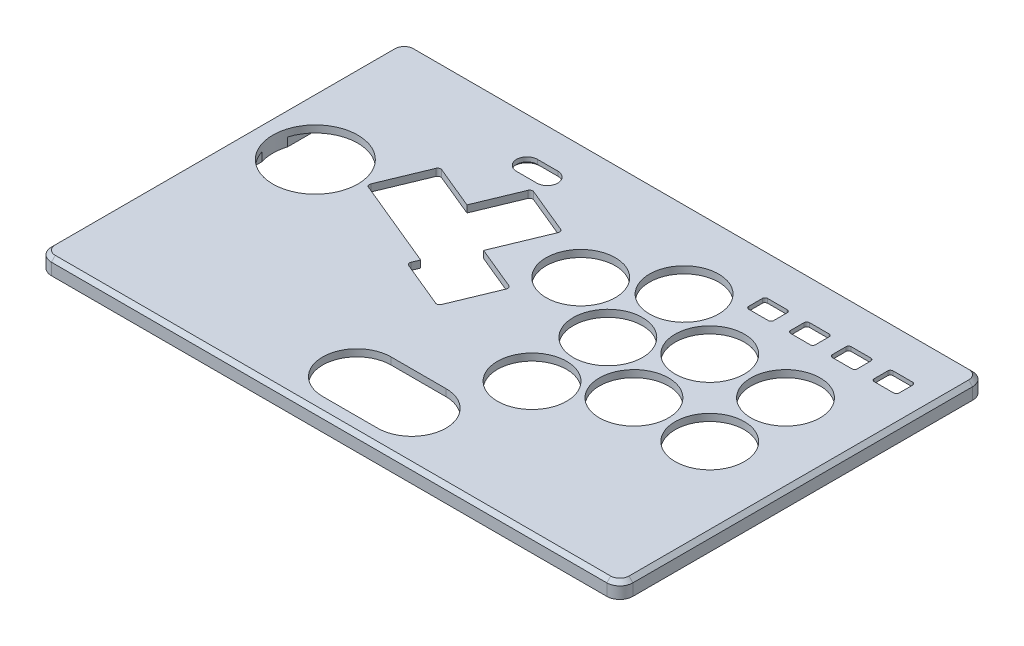
SolidWorks part; units mm, degrees
ref_plane "Front Plane" through (0, 0, 0) normal (0, 0, 1) x (1, 0, 0)
ref_plane "Top Plane" through (0, 0, 0) normal (0, 1, 0) x (1, 0, 0)
ref_plane "Right Plane" through (0, 0, 0) normal (1, 0, 0) x (0, 0, -1)
sketch "Sketch1" plane through (0, 0, 0) normal (0, 1, 0) x (1, 0, 0)
  line L1 (0, 0) -> (222.53, 0)
  line L2 (0, 0) -> (0, 140)
  line L3 (0, 140) -> (222.53, 140)
  line L4 (222.53, 0) -> (222.53, 140)
  line L5 (217.53, 140) -> (50.88, 140) construction
  line L6 (222.53, 5) -> (222.53, 135) construction
extrude "Top Plate" add sketch "Sketch1" along normal blind 6
fillet "Corner Fillet" radius 5 4 edges at (0, 3, -140) (0, 3, 0) (222.53, 3, -140) (222.53, 3, 0)
hole_wizard "M3 Clearance Hole1" positions "3DSketch1" profile "Sketch3" hole size "M3" standard "ANSI Metric"
sketch3d "3DSketch1"
  line L0 (5, 0, 0) -> (217.53, 0, 0) construction
  line L1 (222.53, 0, -5) -> (222.53, 0, -135) construction
  line L2 (217.53, 0, -140) -> (5, 0, -140) construction
  line L3 (0, 0, -135) -> (0, 0, -5) construction
  point P0 (217.03, 0, -5.5)
  point P2 (217.03, 0, -134.5)
  point P4 (5.5, 0, -134.5)
  point P6 (5.5, 0, -5.5)
  dimension "D1" = 5.5
  dimension "D2" = 5.5
  dimension "D3" = 5.5
  dimension "D4" = 5.5
  dimension "D5" = 5.5
  dimension "D6" = 5.5
  dimension "D7" = 5.5
  dimension "D8" = 5.5
sketch "Sketch3" plane through (217.03, 0, -5.5) normal (1, 0, 0) x (0, 0, -1)
  line L0 (0, 0) -> (0, 5.25)
  line L1 (0, 5.25) -> (1.7, 4.2285)
  line L2 (1.7, 4.2285) -> (1.7, 0)
  line L5 (1.7, 0) -> (0, 0)
  line L10 (0, 5.25) -> (-1.7, 4.2285) construction
  line L11 (0, -6.35) -> (0, 107.95) construction
  dimension "Hole Dia." = 3.4
  dimension "Hole Depth" = 5.25
  dimension "Drill Angle" = 118
sketch "Sketch4" plane through (0, 6, 0) normal (0, -1, 0) x (-1, 0, 0)
  line L0 (-94.0588, 59.555) -> (-76.4589, 66.8451) construction
  line L1 (-94.0588, 59.555) -> (-101.349, 77.1549) construction
  line L2 (-76.4589, 66.8451) -> (-77.9897, 70.5406) construction
  line L3 (-101.349, 77.1549) -> (-83.7491, 84.445) construction
  line L4 (-94.0588, 59.555) -> (-83.7491, 84.445) construction
  line L5 (-76.4589, 66.8451) -> (-101.349, 77.1549) construction
  line L6 (-77.9897, 70.5406) -> (-60.3898, 77.8307) construction
  line L7 (-83.7491, 84.445) -> (-85.2798, 88.1405) construction
  line L8 (-60.3898, 77.8307) -> (-67.6799, 95.4306) construction
  line L9 (-85.2798, 88.1405) -> (-67.6799, 95.4306) construction
  line L10 (-77.9897, 70.5406) -> (-67.6799, 95.4306) construction
  line L11 (-60.3898, 77.8307) -> (-85.2798, 88.1405) construction
  line L12 (-60.3898, 77.8307) -> (-42.7899, 85.1209) construction
  line L14 (-42.7899, 85.1209) -> (-50.08, 102.7208) construction
  line L15 (-67.6799, 95.4306) -> (-50.08, 102.7208) construction
  line L16 (-60.3898, 77.8307) -> (-50.08, 102.7208) construction
  line L17 (-42.7899, 85.1209) -> (-67.6799, 95.4306) construction
  line L19 (-67.6799, 95.4306) -> (-74.97, 113.0306) construction
  line L20 (-85.2798, 88.1405) -> (-92.5699, 105.7404) construction
  line L21 (-74.97, 113.0306) -> (-92.5699, 105.7404) construction
  line L22 (-67.6799, 95.4306) -> (-92.5699, 105.7404) construction
  line L23 (-85.2798, 88.1405) -> (-74.97, 113.0306) construction
  line L24 (-5, 0) -> (-217.53, 0) construction
  line L25 (-59.9305, 76.7221) -> (-42.3306, 84.0122)
  line L26 (-41.6812, 85.5801) -> (-48.9713, 103.18)
  line L27 (-67.0304, 96.9985) -> (-50.5392, 103.8294)
  line L28 (-67.0304, 96.9985) -> (-73.8613, 113.4898)
  line L29 (-75.4292, 114.1392) -> (-93.0291, 106.8491)
  line L30 (-86.3884, 87.6813) -> (-93.6786, 105.2812)
  line L31 (-85.3169, 85.0944) -> (-86.3884, 87.6813)
  line L32 (-101.8082, 78.2635) -> (-85.3169, 85.0944)
  line L33 (-95.1675, 59.0958) -> (-102.4576, 76.6957)
  line L34 (-93.5996, 58.4463) -> (-75.9997, 65.7365)
  line L35 (-75.3503, 67.3043) -> (-76.4218, 69.8912)
  line L36 (-76.4218, 69.8912) -> (-59.9305, 76.7221)
  line L37 (-66.5712, 95.8899) -> (-74.3206, 114.5984) construction
  line L38 (-68.1391, 96.5393) -> (-49.4305, 104.2886) construction
  line L39 (-74.3206, 114.5984) -> (-94.1378, 106.3899) construction
  line L40 (-86.3884, 87.6813) -> (-94.1378, 106.3899) construction
  line L41 (-102.9168, 77.8043) -> (-85.3169, 85.0944) construction
  line L42 (-94.7083, 57.9871) -> (-102.9168, 77.8043) construction
  line L43 (-94.7083, 57.9871) -> (-74.8911, 66.1957) construction
  line L44 (-74.8911, 66.1957) -> (-76.4218, 69.8912) construction
  line L45 (-59.9305, 76.7221) -> (-41.222, 84.4714) construction
  line L46 (-41.222, 84.4714) -> (-49.4305, 104.2886) construction
  line L47 (-123.9039, 19) -> (-102.9039, 19) construction
  line L48 (-123.9039, 32.1) -> (-102.9039, 32.1)
  line L49 (-123.9039, 5.9) -> (-102.9039, 5.9)
  circle A0 centre (-23, 83.0083) radius 16.25
  circle A1 centre (-137.9339, 51) radius 13.25
  circle A2 centre (-162.9339, 65) radius 13.25
  circle A3 centre (-191.9339, 65) radius 13.25
  circle A4 centre (-191.9339, 94) radius 13.25
  circle A5 centre (-162.9339, 94) radius 13.25
  circle A6 centre (-137.9339, 80) radius 13.25
  circle A7 centre (-138.1143, 108.9994) radius 13.25
  circle A8 centre (-112.9159, 94.6459) radius 13.25
  arc A9 (-93.0291, 106.8491) -> (-93.6786, 105.2812) centre (-92.5699, 105.7404) ccw
  arc A10 (-101.8082, 78.2635) -> (-102.4576, 76.6957) centre (-101.349, 77.1549) ccw
  arc A11 (-95.1675, 59.0958) -> (-93.5996, 58.4463) centre (-94.0588, 59.555) ccw
  arc A12 (-75.9997, 65.7365) -> (-75.3503, 67.3043) centre (-76.4589, 66.8451) ccw
  arc A13 (-42.3306, 84.0122) -> (-41.6812, 85.5801) centre (-42.7899, 85.1209) ccw
  arc A14 (-73.8613, 113.4898) -> (-75.4292, 114.1392) centre (-74.97, 113.0306) ccw
  arc A15 (-48.9713, 103.18) -> (-50.5392, 103.8294) centre (-50.08, 102.7208) ccw
  arc A16 (-123.9039, 32.1) -> (-123.9039, 5.9) centre (-123.9039, 19) ccw
  arc A17 (-102.9039, 5.9) -> (-102.9039, 32.1) centre (-102.9039, 19) ccw
  point P28 (-88.9039, 72)
  point P29 (-72.8348, 82.9856)
  point P30 (-55.2349, 90.2758)
  point P35 (-80.1249, 100.5855)
  point P90 (-113.4039, 19)
  point P96 (-89.8039, 19)
  point P97 (-137.0039, 19)
  dimension "D1" = 32.5
  dimension "D2" = 26.5
  dimension "D6" = 1.2
  dimension "D8" = 13.1
  dimension "D3" = 22.5
  dimension "D4" = 19.05
  dimension "D5" = 1.2
  dimension "D7" = 47.2
extrude "Primary Buttons" cut sketch "Sketch4" along normal blind 10 contours A15 L26 A13 L25 L36 L35 A12 L34 A11 L33 A10 L32 L31 L30 A9 L29 A14 L28 L27 | A0 | A8 | A7 | A5 | A4 | A6 | A1 | A2 | A3 | A17 L49 A16 L48
sketch "Sketch5" plane through (0, 0, 0) normal (0, -1, 0) x (1, 0, 0)
  line L2 (154.55, -122.52) -> (154.55, -117.32)
  line L3 (155.55, -116.32) -> (163.05, -116.32)
  line L4 (164.05, -122.52) -> (164.05, -117.32)
  line L5 (154.55, -123.52) -> (164.05, -116.32) construction
  line L6 (154.55, -116.32) -> (164.05, -123.52) construction
  line L7 (155.55, -123.52) -> (163.05, -123.52)
  line L8 (170.55, -122.52) -> (170.55, -117.32)
  line L9 (171.55, -116.32) -> (179.05, -116.32)
  line L10 (180.05, -122.52) -> (180.05, -117.32)
  line L11 (171.55, -123.52) -> (179.05, -123.52)
  line L12 (170.55, -123.52) -> (180.05, -116.32) construction
  line L13 (170.55, -116.32) -> (180.05, -123.52) construction
  line L14 (186.55, -122.52) -> (186.55, -117.32)
  line L15 (187.55, -116.32) -> (195.05, -116.32)
  line L16 (196.05, -122.52) -> (196.05, -117.32)
  line L17 (187.55, -123.52) -> (195.05, -123.52)
  line L18 (186.55, -123.52) -> (196.05, -116.32) construction
  line L19 (186.55, -116.32) -> (196.05, -123.52) construction
  line L20 (202.55, -122.52) -> (202.55, -117.32)
  line L21 (203.55, -116.32) -> (211.05, -116.32)
  line L22 (212.05, -122.52) -> (212.05, -117.32)
  line L23 (203.55, -123.52) -> (211.05, -123.52)
  line L24 (202.55, -123.52) -> (212.05, -116.32) construction
  line L25 (202.55, -116.32) -> (212.05, -123.52) construction
  line L26 (159.3, -119.92) -> (160, -119.92) construction
  arc A0 (163.05, -123.52) -> (164.05, -122.52) centre (163.05, -122.52) ccw
  arc A1 (155.55, -123.52) -> (154.55, -122.52) centre (155.55, -122.52) cw
  arc A2 (154.55, -117.32) -> (155.55, -116.32) centre (155.55, -117.32) cw
  arc A3 (163.05, -116.32) -> (164.05, -117.32) centre (163.05, -117.32) cw
  arc A4 (179.05, -123.52) -> (180.05, -122.52) centre (179.05, -122.52) ccw
  arc A5 (171.55, -123.52) -> (170.55, -122.52) centre (171.55, -122.52) cw
  arc A6 (170.55, -117.32) -> (171.55, -116.32) centre (171.55, -117.32) cw
  arc A7 (179.05, -116.32) -> (180.05, -117.32) centre (179.05, -117.32) cw
  arc A8 (195.05, -123.52) -> (196.05, -122.52) centre (195.05, -122.52) ccw
  arc A9 (187.55, -123.52) -> (186.55, -122.52) centre (187.55, -122.52) cw
  arc A10 (186.55, -117.32) -> (187.55, -116.32) centre (187.55, -117.32) cw
  arc A11 (195.05, -116.32) -> (196.05, -117.32) centre (195.05, -117.32) cw
  arc A12 (211.05, -123.52) -> (212.05, -122.52) centre (211.05, -122.52) ccw
  arc A13 (203.55, -123.52) -> (202.55, -122.52) centre (203.55, -122.52) cw
  arc A14 (202.55, -117.32) -> (203.55, -116.32) centre (203.55, -117.32) cw
  arc A15 (211.05, -116.32) -> (212.05, -117.32) centre (211.05, -117.32) cw
  point P0 (159.3, -119.92)
  point P7 (175.3, -119.92)
  point P39 (191.3, -119.92)
  point P56 (207.3, -119.92)
  dimension "D1" = 7.2
  dimension "D3" = 1
  dimension "D2" = 9.5
  dimension "D5" = 16
  dimension "D6" = 0.7
  dimension "D4" = 4
extrude "Extra Buttons" cut sketch "Sketch5" against normal up to next
sketch "Sketch8" plane through (0, 0, 0) normal (0, -1, 0) x (1, 0, 0)
  line L24 (215.03, -132.5) -> (215.03, -7.5)
  line L25 (7.5, -132.5) -> (215.03, -132.5)
  line L26 (7.5, -7.5) -> (7.5, -132.5)
  line L27 (215.03, -7.5) -> (7.5, -7.5)
  line L28 (215.03, -132.5) -> (215.03, -7.5)
  line L29 (7.5, -132.5) -> (215.03, -132.5)
  line L30 (7.5, -7.5) -> (7.5, -132.5)
  line L31 (215.03, -7.5) -> (7.5, -7.5)
  dimension "D1" = 7.5
extrude "Hollow Out" cut sketch "Sketch8" against normal blind 3.3
fillet "Fillet1" radius 10 3 edges at (7.5, 1.65, -132.5) (7.5, 1.65, -7.5) (215.03, 1.65, -7.5)
fillet "Fillet2" radius 5 1 edges at (215.03, 1.65, -132.5)
sketch "Sketch15" plane through (0, 0, 0) normal (0, -1, 0) x (1, 0, 0)
  line L0 (163.05, -116.32) -> (155.55, -116.32) construction
  line L1 (151.3, -127.92) -> (215.3, -127.92)
  line L2 (151.3, -127.92) -> (151.3, -111.92)
  line L3 (151.3, -111.92) -> (215.3, -111.92)
  line L4 (215.3, -127.92) -> (215.3, -111.92)
  line L5 (154.55, -117.32) -> (154.55, -122.52) construction
  line L6 (211.05, -116.32) -> (203.55, -116.32) construction
  point P4 (159.3, -119.92)
  point P5 (207.3, -119.92)
  point P10 (159.3, -116.32)
  point P13 (154.55, -119.92)
  point P18 (207.3, -116.32)
  dimension "D1" = 8
  dimension "D2" = 8
  dimension "D3" = 8
  dimension "D4" = 8
extrude "Cut-Extrude4" cut sketch "Sketch15" against normal blind 4.4
sketch "Sketch9" plane through (0, 6, 0) normal (0, 1, 0) x (1, 0, 0)
  line L0 (68.26, 121.5875) -> (70.35, 121.5875) construction
  line L1 (70.6, 121.1545) -> (70.1, 122.0205) construction
  line L2 (68.51, 122.0205) -> (68.01, 121.1545) construction
  line L3 (65.42, 121.5875) -> (73.19, 121.5875) construction
  line L4 (65.42, 125.5875) -> (73.19, 125.5875)
  line L5 (65.42, 117.5875) -> (73.19, 117.5875)
  arc A0 (65.42, 125.5875) -> (65.42, 117.5875) centre (65.42, 121.5875) ccw
  arc A1 (73.19, 117.5875) -> (73.19, 125.5875) centre (73.19, 121.5875) ccw
  point P8 (69.305, 121.5875)
  dimension "D2" = 4
  dimension "D1" = 7.77
extrude "Light Guide Cutout" cut sketch "Sketch9" against normal blind 10
chamfer "Chamfer1" distance 1 angle 45 4 edges at (77.19, 3.3, -121.5875) (69.305, 3.3, -117.5875) (61.42, 3.3, -121.5875) (69.305, 3.3, -125.5875)
chamfer "Top Chamfer" distance 1.5 angle 45 8 edges at (221.0655, 6, -138.5355) (222.53, 6, -70) (221.0655, 6, -1.4645) (111.265, 6, -140) (1.4645, 6, -138.5355) (0, 6, -70) (1.4645, 6, -1.4645) (111.265, 6, 0)
sketch "Sketch11" plane through (0, 0, 0) normal (0, -1, 0) x (1, 0, 0)
  line L0 (217.03, -138.6012) -> (212.9288, -134.5)
  line L1 (217.03, -138.6012) -> (221.1312, -134.5)
  line L2 (212.9288, -134.5) -> (217.03, -130.3988)
  line L3 (221.1312, -134.5) -> (217.03, -130.3988)
  line L4 (217.03, -138.6012) -> (217.03, -130.3988) construction
  line L5 (212.9288, -134.5) -> (221.1312, -134.5) construction
  line L6 (1.3988, -134.5) -> (5.5, -130.3988)
  line L7 (1.3988, -134.5) -> (5.5, -138.6012)
  line L8 (5.5, -130.3988) -> (9.6012, -134.5)
  line L9 (5.5, -138.6012) -> (9.6012, -134.5)
  line L10 (1.3988, -134.5) -> (9.6012, -134.5) construction
  line L11 (5.5, -130.3988) -> (5.5, -138.6012) construction
  line L12 (5.5, -9.6012) -> (1.3988, -5.5)
  line L13 (5.5, -9.6012) -> (9.6012, -5.5)
  line L14 (1.3988, -5.5) -> (5.5, -1.3988)
  line L15 (9.6012, -5.5) -> (5.5, -1.3988)
  line L16 (5.5, -9.6012) -> (5.5, -1.3988) construction
  line L17 (1.3988, -5.5) -> (9.6012, -5.5) construction
  line L18 (217.03, -9.6012) -> (212.9288, -5.5)
  line L19 (217.03, -9.6012) -> (221.1312, -5.5)
  line L20 (212.9288, -5.5) -> (217.03, -1.3988)
  line L21 (221.1312, -5.5) -> (217.03, -1.3988)
  line L22 (217.03, -9.6012) -> (217.03, -1.3988) construction
  line L23 (212.9288, -5.5) -> (221.1312, -5.5) construction
  line L24 (217.53, -140) -> (5, -140) construction
  point P1 (217.03, -134.5)
  point P2 (5.5, -134.5)
  point P3 (5.5, -5.5)
  point P8 (217.03, -5.5)
  dimension "D1" = 45
  dimension "D2" = 5.8
extrude "Nut Cutout" cut sketch "Sketch11" against normal blind 2 from offset 1.2 offset against normal yes
sketch "Sketch16" plane through (0, 0, 0) normal (0, -1, 0) x (1, 0, 0)
  line L0 (217.53, -140) -> (5, -140) construction
  line L1 (90, -111) -> (118, -111)
  line L2 (90, -111) -> (90, -131)
  line L3 (90, -131) -> (132.53, -131)
  line L8 (118, -111) -> (132.53, -131)
  line L11 (0, -135) -> (0, -5) construction
  line L12 (222.53, -5) -> (222.53, -135) construction
  dimension "D1" = 9
  dimension "D2" = 90
  dimension "D3" = 90
  dimension "D4" = 20
  dimension "D5" = 28
extrude "Host USB Cutout" [suppressed] cut sketch "Sketch16" against normal blind 3.5
chamfer "Chamfer4" [suppressed] distance 2 angle 45
fillet "Top Fillet" [suppressed] radius 1.5
sketch "Sketch17" plane through (0, 6, 0) normal (0, 1, 0) x (1, 0, 0)
  line L1 (1.5, 135) -> (5, 135)
  line L2 (1.5, 135) -> (1.5, 140)
  line L3 (1.5, 140) -> (5, 140)
  line L4 (5, 135) -> (5, 140)
  line L5 (1.5, 140) -> (41.5, 140)
  line L6 (1.5, 140) -> (1.5, 180)
  line L7 (1.5, 180) -> (41.5, 180)
  line L8 (41.5, 140) -> (41.5, 180)
  line L9 (1.5, 5) -> (5, 5)
  line L10 (1.5, 5) -> (1.5, 0)
  line L11 (1.5, 0) -> (5, 0)
  line L12 (5, 5) -> (5, 0)
  line L13 (1.5, 0) -> (41.5, 0)
  line L14 (1.5, 0) -> (1.5, -40)
  line L15 (1.5, -40) -> (41.5, -40)
  line L16 (41.5, 0) -> (41.5, -40)
  line L17 (221.03, 5) -> (217.53, 5)
  line L18 (221.03, 5) -> (221.03, 0)
  line L19 (221.03, 0) -> (217.53, 0)
  line L20 (217.53, 5) -> (217.53, 0)
  line L21 (221.03, 0) -> (181.03, 0)
  line L22 (221.03, 0) -> (221.03, -40)
  line L23 (221.03, -40) -> (181.03, -40)
  line L24 (181.03, 0) -> (181.03, -40)
  line L25 (221.03, 135) -> (217.53, 135)
  line L26 (221.03, 135) -> (221.03, 140)
  line L27 (221.03, 140) -> (217.53, 140)
  line L28 (217.53, 135) -> (217.53, 140)
  line L29 (221.03, 140) -> (181.03, 140)
  line L30 (221.03, 140) -> (221.03, 180)
  line L31 (221.03, 180) -> (181.03, 180)
  line L32 (181.03, 140) -> (181.03, 180)
  dimension "D1" = 40
  dimension "D2" = 5
extrude "top Build plate adhesion" [suppressed] add sketch "Sketch17" against normal blind 0.6 contours L21 L24 L23 L22 L19 | L16 L13 L11 L14 L15 | L12 L9 L10 L11 | L17 L20 L19 L18 | L5 L8 L7 L6 L3 | L32 L29 L27 L30 L31 | L28 L25 L26 L27 | L1 L4 L3 L2
fillet "Fillet3" [suppressed] radius 20
sketch "Sketch18" plane through (0, 0, 0) normal (0, -1, 0) x (1, 0, 0)
  line L0 (217.53, -140) -> (5, -140) construction
  line L1 (0, -5) -> (2, -5)
  line L2 (0, -5) -> (0, 1)
  line L3 (0, 1) -> (5, 1)
  line L4 (5, -2) -> (5, 1)
  line L5 (222.53, -5) -> (220.53, -5)
  line L6 (222.53, -5) -> (222.53, 1)
  line L7 (222.53, 1) -> (217.53, 1)
  line L8 (217.53, -2) -> (217.53, 1)
  line L9 (222.53, -135) -> (217.53, -135)
  line L10 (222.53, -135) -> (222.53, -141)
  line L11 (222.53, -141) -> (214.53, -141)
  line L12 (214.53, -138) -> (214.53, -141)
  line L13 (0, -135) -> (5, -135)
  line L14 (0, -135) -> (0, -141)
  line L15 (0, -141) -> (8, -141)
  line L16 (8, -138) -> (8, -141)
  line L17 (0, 1) -> (40, 1)
  line L18 (0, 1) -> (0, 41)
  line L19 (0, 41) -> (40, 41)
  line L20 (40, 1) -> (40, 41)
  line L21 (222.53, 1) -> (182.53, 1)
  line L22 (222.53, 1) -> (222.53, 41)
  line L23 (222.53, 41) -> (182.53, 41)
  line L24 (182.53, 1) -> (182.53, 41)
  line L25 (222.53, -141) -> (182.53, -141)
  line L26 (222.53, -141) -> (222.53, -181)
  line L27 (222.53, -181) -> (182.53, -181)
  line L28 (182.53, -141) -> (182.53, -181)
  line L29 (0, -141) -> (40, -141)
  line L30 (0, -141) -> (0, -181)
  line L31 (0, -181) -> (40, -181)
  line L32 (40, -141) -> (40, -181)
  arc A0 (220.53, -5) -> (217.53, -2) centre (220.53, -2) cw
  arc A1 (2, -5) -> (5, -2) centre (2, -2) ccw
  arc A2 (5, -135) -> (8, -138) centre (5, -138) cw
  arc A3 (217.53, -135) -> (214.53, -138) centre (217.53, -138) ccw
  arc M49 (0, -135) -> (5, -140) centre (5, -135) ccw
  line M50 (5, -140) -> (217.53, -140)
  arc M51 (217.53, -140) -> (222.53, -135) centre (217.53, -135) ccw
  dimension "D4" = 3
  dimension "D1" = 40
  dimension "D2" = 5
  dimension "D3" = 1
extrude "Boss-Extrude1" [suppressed] add sketch "Sketch18" against normal blind 0.6 contours L25 L28 L27 L26 L11 | L32 L29 L15 L30 L31 | L16 L14 L15 M50 M49 | L12 L11 L10 M50 M51 | L24 L21 L7 L22 L23 | L17 L20 L19 L18 L3
fillet "Fillet4" [suppressed] radius 20
